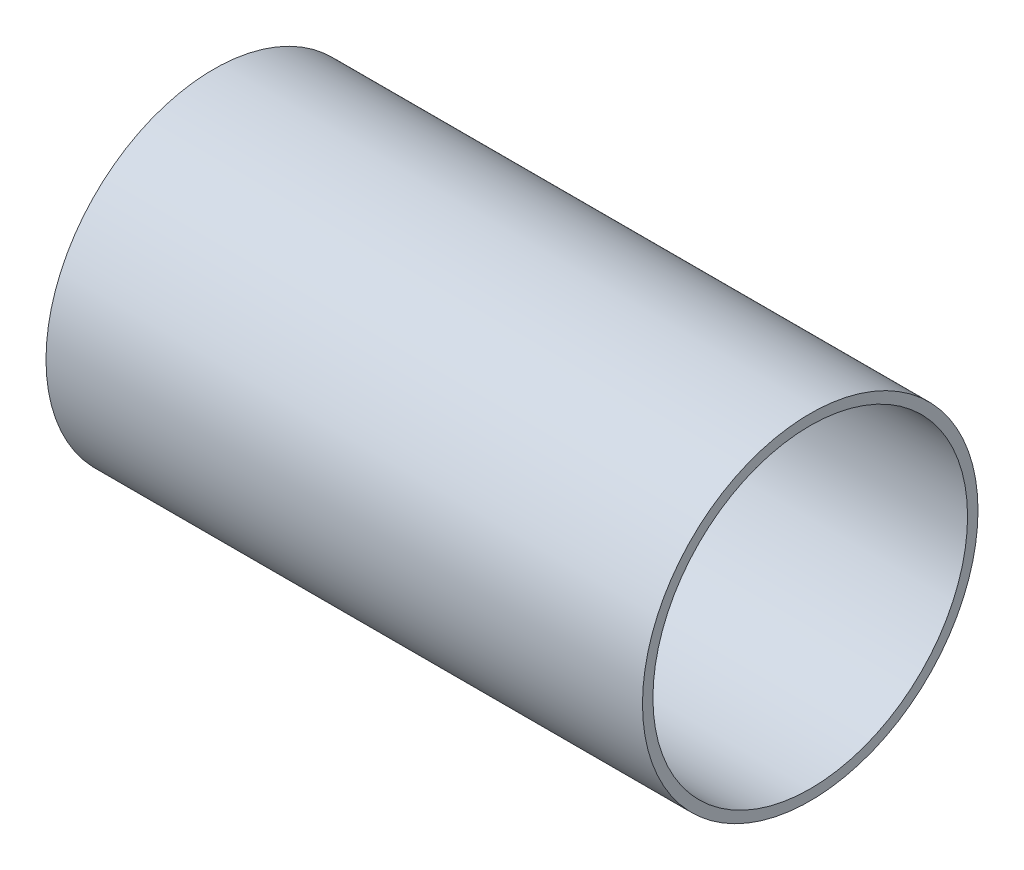
SolidWorks part; units mm, degrees
material "Copper"
ref_plane "Front" through (0, 0, 0) normal (0, 0, 1) x (1, 0, 0)
ref_plane "Top" through (0, 0, 0) normal (0, 1, 0) x (1, 0, 0)
ref_plane "Right" through (0, 0, 0) normal (1, 0, 0) x (0, 0, -1)
sketch "Sketch1" plane through (0, 0, 0) normal (1, 0, 0) x (0, 0, -1)
  circle A0 centre (0, 0) radius 14.2875
  circle A1 centre (0, 0) radius 13.3985
  point P4 (14.2875, 0)
  point P5 (13.3985, 0)
  dimension "OD" = 28.575
  dimension "ID" = 26.797
  dimension "Wall" = 0.889
extrude "Extrude1" add sketch "Sketch1" along normal mid plane 50.8
sketch "Sketch2" plane through (0, 0, 0) normal (0, 0, 1) x (1, 0, 0)
  line L0 (-25.4, 0) -> (25.4, 0) construction
  line L1 (-25.4, 14.2875) -> (-25.4, -14.2875) construction
